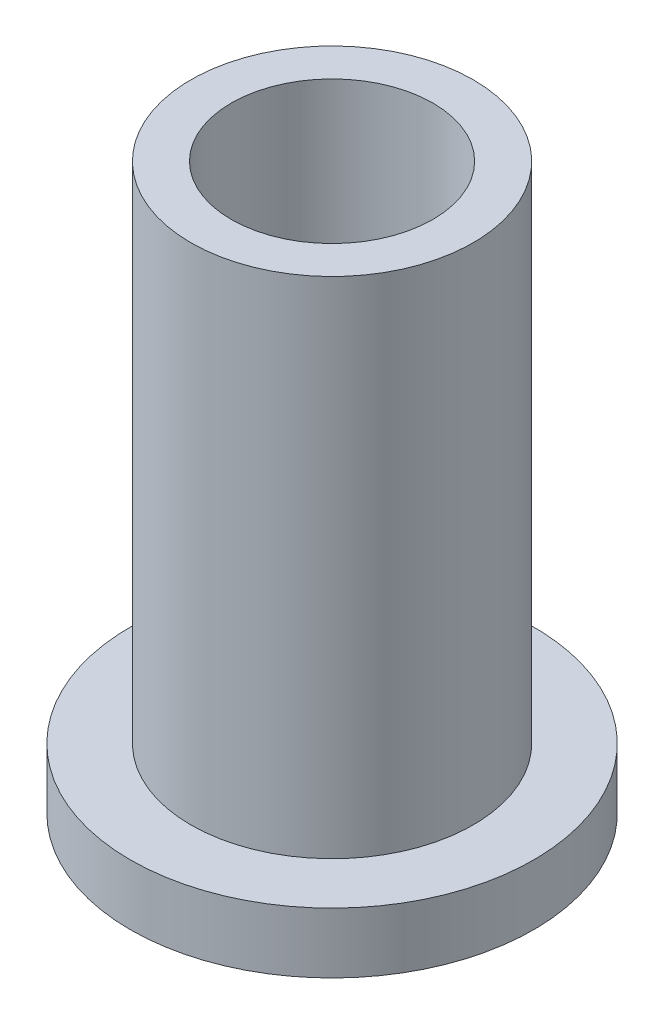
SolidWorks part; units mm, degrees
ref_plane "Front Plane" through (0, 0, 0) normal (0, 0, 1) x (1, 0, 0)
ref_plane "Top Plane" through (0, 0, 0) normal (0, 1, 0) x (1, 0, 0)
ref_plane "Right Plane" through (0, 0, 0) normal (1, 0, 0) x (0, 0, -1)
sketch "Sketch1" plane through (0, 0, 0) normal (0, 1, 0) x (1, 0, 0)
  circle A0 centre (0, 0) radius 5
  dimension "D1" = 10
extrude "Boss-Extrude1" add sketch "Sketch1" along normal blind 1.5
sketch "Sketch2" plane through (0, 1.5, 0) normal (0, 1, 0) x (1, 0, 0)
  circle A0 centre (0, 0) radius 3.5
  dimension "D1" = 7
extrude "Boss-Extrude2" add sketch "Sketch2" along normal blind 12.5
sketch "Sketch3" plane through (0, 14, 0) normal (0, 1, 0) x (1, 0, 0)
  circle A0 centre (0, 0) radius 2.5
  dimension "D1" = 5
extrude "Cut-Extrude1" cut sketch "Sketch3" against normal through all
